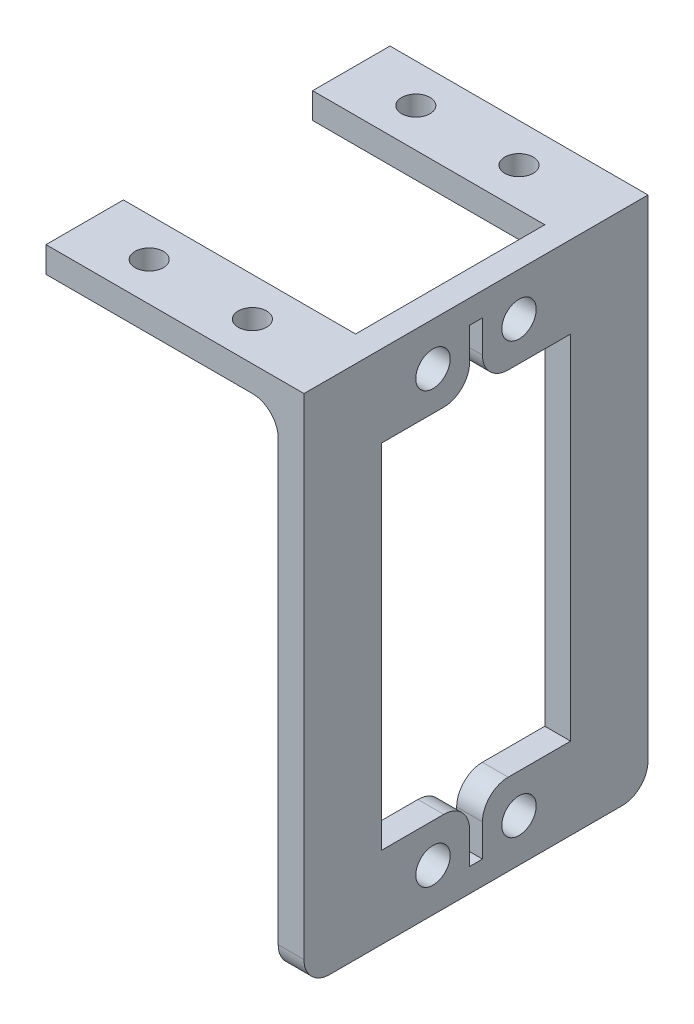
SolidWorks part; units mm, degrees
ref_plane "前视基准面" through (0, 0, 0) normal (0, 0, 1) x (1, 0, 0)
ref_plane "上视基准面" through (0, 0, 0) normal (0, 1, 0) x (1, 0, 0)
ref_plane "右视基准面" through (0, 0, 0) normal (1, 0, 0) x (0, 0, -1)
sketch "草图1" plane through (0, 0, 0) normal (0, 0, 1) x (1, 0, 0)
  line L0 (0, 0) -> (30, 0)
  line L1 (30, 0) -> (30, -60)
  line L2 (0, -3) -> (27, -3)
  line L3 (27, -3) -> (27, -60)
  line L4 (27, -60) -> (30, -60)
  line L5 (0, 0) -> (0, -3)
  dimension "D1" = 30
  dimension "D3" = 60
  dimension "D2" = 3
extrude "凸台-拉伸1" add sketch "草图1" along normal blind 40
sketch "草图2" plane through (0, 0, 0) normal (0, 1, 0) x (1, 0, 0)
  line L0 (0, 0) -> (0, -9) construction
  line L1 (0, -40) -> (0, 0) construction
  line L2 (0, -9) -> (27, -9)
  line L3 (30, -40) -> (30, 0) construction
  line L4 (27, -9) -> (27, 0) construction
  line L5 (27, 0) -> (0, 0) construction
  line L6 (0, -20) -> (30, -20) construction
  line L7 (27, -31) -> (27, -40) construction
  line L8 (0, -31) -> (27, -31)
  line L9 (0, -40) -> (0, -31) construction
  line L10 (27, -40) -> (0, -40) construction
  line L11 (27, -40) -> (27, 0) construction
  line L12 (27, -9) -> (27, -31)
  line L13 (0, -9) -> (0, -31)
  line L14 (7.5, -4.5) -> (19.5, -4.5) construction
  line L15 (13.5, -4.5) -> (13.5, 0) construction
  line L16 (13.5, -4.5) -> (13.5, -9) construction
  circle A0 centre (7.5, -4.5) radius 1.65
  circle A1 centre (19.5, -4.5) radius 1.65
  circle A2 centre (19.5, -35.5) radius 1.65
  circle A3 centre (7.5, -35.5) radius 1.65
  dimension "D2" = 3.3
  dimension "D3" = 12
  dimension "D1" = 9
extrude "切除-拉伸2" cut sketch "草图2" against normal blind 10
sketch "草图3" plane through (30, 0, 0) normal (1, 0, 0) x (0, 0, -1)
  line L0 (-20, 0) -> (-20, -71.9676) construction
  line L1 (-40, 0) -> (0, 0) construction
  line L2 (-25, -5) -> (-15, -5) construction
  line L3 (-40, -3) -> (-31, -3) construction
  line L4 (-15, -5) -> (-15, -55) construction
  line L5 (-15, -30) -> (-20, -30) construction
  line L6 (-20.75, -9.5) -> (-20.75, -2.75)
  line L7 (-31, -50.5) -> (-20.75, -50.5)
  line L8 (-31, -50.5) -> (-31, -9.5)
  line L9 (-31, -9.5) -> (-20.75, -9.5)
  line L10 (-9, -50.5) -> (-9, -9.5)
  line L11 (-31, -50.5) -> (-9, -9.5) construction
  line L12 (-31, -9.5) -> (-9, -50.5) construction
  line L13 (-20.75, -2.75) -> (-19.25, -2.75)
  line L14 (-19.25, -2.75) -> (-19.25, -9.5)
  line L15 (-20.75, -57.25) -> (-19.25, -57.25)
  line L16 (-20.75, -50.5) -> (-20.75, -57.25)
  line L17 (-19.25, -57.25) -> (-19.25, -50.5)
  line L18 (-19.25, -50.5) -> (-9, -50.5)
  line L19 (-19.25, -9.5) -> (-9, -9.5)
  circle A0 centre (-25, -5) radius 2
  circle A1 centre (-15, -5) radius 2
  circle A2 centre (-15, -55) radius 2
  circle A3 centre (-25, -55) radius 2
  dimension "D3" = 4
  dimension "D4" = 50
  dimension "D1" = 10
  dimension "D2" = 2
  dimension "D5" = 22
  dimension "D6" = 41
  dimension "D7" = 1.5
  dimension "D8" = 6.75
extrude "切除-拉伸3" cut sketch "草图3" against normal blind 10
fillet "圆角1" radius 3 8 edges at (27, -3, 4.5) (27, -3, 35.5) (28.5, -60, 40) (28.5, -60, 0) (28.5, -9.5, 19.25) (28.5, -9.5, 20.75) (28.5, -50.5, 19.25) (28.5, -50.5, 20.75)
